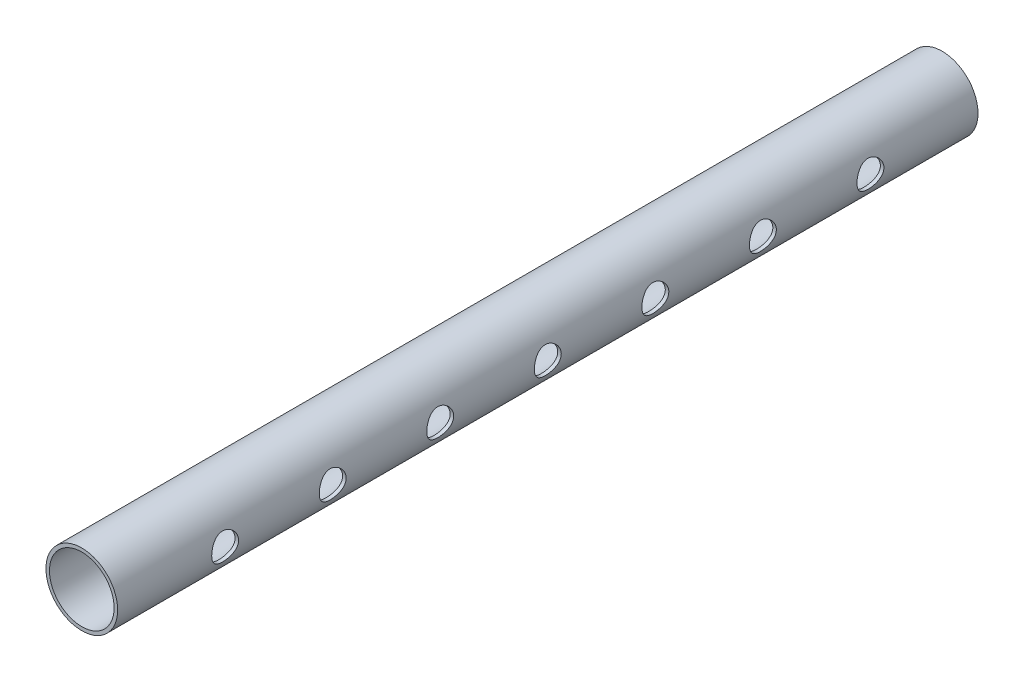
SolidWorks part; units mm, degrees
material "Plain Carbon Steel"
ref_plane "Front" through (0, 0, 0) normal (0, 0, 1) x (1, 0, 0)
ref_plane "Top" through (0, 0, 0) normal (0, 1, 0) x (1, 0, 0)
ref_plane "Right" through (0, 0, 0) normal (1, 0, 0) x (0, 0, -1)
sketch "Sketch1" plane through (0, 0, 0) normal (0, 0, 1) x (1, 0, 0)
  circle A0 centre (0, 0) radius 12.7
  circle A1 centre (0, 0) radius 11.4554
  dimension "D1" = 1.2446
  dimension "D2" = 25.4
extrude "Boss-Extrude1" add sketch "Sketch1" along normal mid plane 304.8
ref_plane "Plane1" through (25.4, 0, 0) normal (1, 0, 0) x (0, 0, -1)
sketch "Sketch2" plane through (25.4, 0, 0) normal (1, 0, 0) x (0, 0, -1)
  line L0 (-152.4, 12.7) -> (-152.4, -12.7) construction
  line L1 (152.4, -12.7) -> (152.4, 12.7) construction
  line L2 (-152.4, 12.7) -> (-152.4, -12.7) construction
  line L3 (152.4, -12.7) -> (152.4, 12.7) construction
  line L4 (-152.4, 0) -> (152.4, 0) construction
  circle A0 centre (0, 0) radius 4.7625
  circle A1 centre (38.1, 0) radius 4.7625
  circle A2 centre (76.2, 0) radius 4.7625
  circle A3 centre (114.3, 0) radius 4.7625
  circle A4 centre (-38.1, 0) radius 4.7625
  circle A5 centre (-76.2, 0) radius 4.7625
  circle A6 centre (-114.3, 0) radius 4.7625
  dimension "D1" = 9.525
  dimension "D2" = 4
  dimension "D3" = 4
  dimension "D4" = 38.1
  dimension "D5" = 38.1
extrude "Cut-Extrude1" cut sketch "Sketch2" against normal through all
